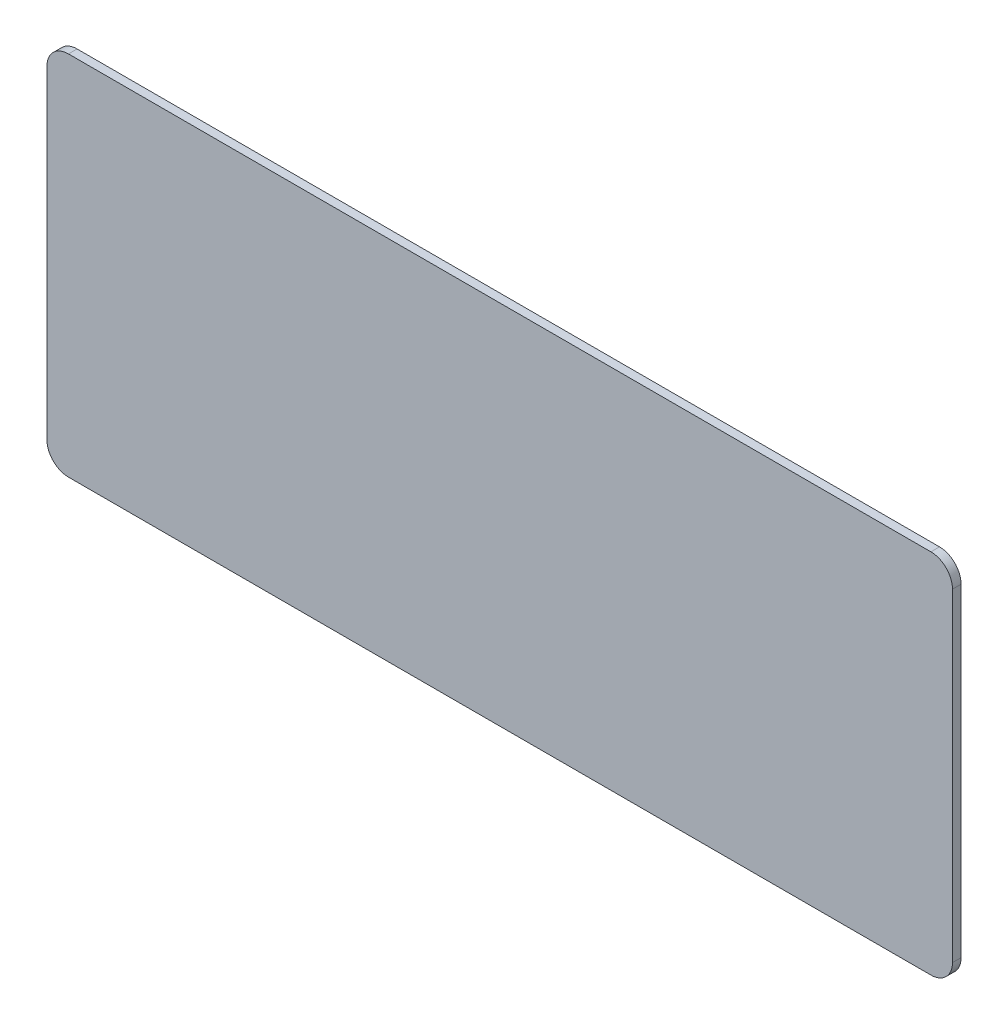
SolidWorks part; units mm, degrees
ref_plane "Front Plane" through (0, 0, 0) normal (0, 0, 1) x (1, 0, 0)
ref_plane "Top Plane" through (0, 0, 0) normal (0, 1, 0) x (1, 0, 0)
ref_plane "Right Plane" through (0, 0, 0) normal (1, 0, 0) x (0, 0, -1)
sketch "Sketch1" plane through (0, 0, 0) normal (0, 0, 1) x (1, 0, 0)
  line L1 (0, 0) -> (53.34, 0)
  line L2 (0, 0) -> (0, 21.59)
  line L3 (0, 21.59) -> (53.34, 21.59)
  line L4 (53.34, 0) -> (53.34, 21.59)
  dimension "D1" = 53.34
  dimension "D2" = 21.59
extrude "Extrude1" add sketch "Sketch1" along normal blind 0.508
ref_plane "Plane1" through (26.67, 0, 0) normal (-1, 0, 0) x (0, 0, 1)
ref_plane "Plane2" through (0, 10.795, 0) normal (0, -1, 0) x (1, 0, 0)
fillet "Fillet1" radius 1.27 4 edges at (0, 21.59, 0.254) (53.34, 21.59, 0.254) (53.34, 0, 0.254) (0, 0, 0.254)
